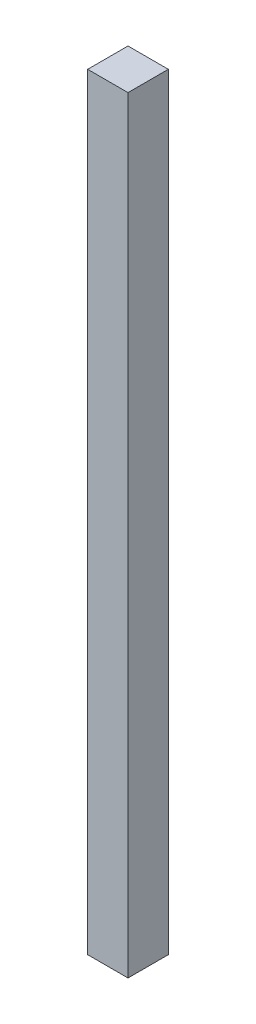
SolidWorks part; units mm, degrees
ref_plane "Front Plane" through (0, 0, 0) normal (0, 0, 1) x (1, 0, 0)
ref_plane "Top Plane" through (0, 0, 0) normal (0, 1, 0) x (1, 0, 0)
ref_plane "Right Plane" through (0, 0, 0) normal (1, 0, 0) x (0, 0, -1)
sketch "Sketch1" plane through (0, 0, 0) normal (0, 1, 0) x (1, 0, 0)
  line L1 (0, 0) -> (25.4, 0)
  line L2 (0, 0) -> (0, 25.4)
  line L3 (0, 25.4) -> (25.4, 25.4)
  line L4 (25.4, 0) -> (25.4, 25.4)
  dimension "D1" = 25.4
  dimension "D2" = 25.4
extrude "Boss-Extrude1" add sketch "Sketch1" along normal blind 482.854
